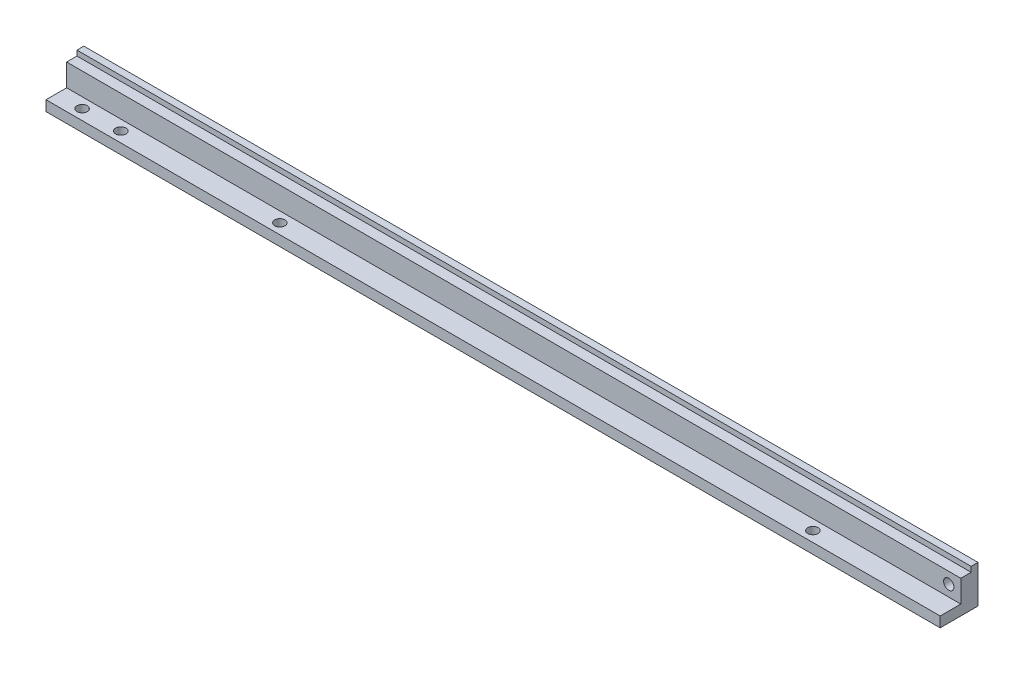
SolidWorks part; units mm, degrees
ref_plane "Спереди" through (0, 0, 0) normal (0, 0, 1) x (1, 0, 0)
ref_plane "Сверху" through (0, 0, 0) normal (0, 1, 0) x (1, 0, 0)
ref_plane "Справа" through (0, 0, 0) normal (1, 0, 0) x (0, 0, -1)
sketch "Эскиз1" plane through (0, 0, 0) normal (1, 0, 0) x (0, 0, -1)
  line L0 (0, 0) -> (-11, 0)
  line L1 (-11, 0) -> (-11, 3)
  line L2 (-11, 3) -> (-5, 3)
  line L3 (-5, 3) -> (-5, 9.5)
  line L4 (-5, 9.5) -> (-2, 9.5)
  line L5 (-2, 9.5) -> (-2, 11)
  line L6 (-2, 11) -> (0, 11)
  line L7 (0, 11) -> (0, 0)
  dimension "D1" = 5
  dimension "D2" = 11
  dimension "D3" = 3
  dimension "D4" = 6
  dimension "D5" = 6.5
  dimension "D6" = 11
  dimension "D7" = 1.5
  dimension "D8" = 2
extrude "Бобышка-Вытянуть1" add sketch "Эскиз1" along normal blind 260
sketch "Эскиз2" plane through (0, 0, 5) normal (0, 0, 1) x (1, 0, 0)
  line L1 (260, 9.5) -> (0, 9.5) construction
  line L2 (260, 9.5) -> (260, 3) construction
  circle A0 centre (256.5, 6.25) radius 1.5
  dimension "D1" = 3
  dimension "D2" = 3.5
  dimension "D3" = 3.25
extrude "Вырез-Вытянуть1" cut sketch "Эскиз2" against normal through all
sketch "Эскиз3" plane through (0, 3, 0) normal (0, 1, 0) x (1, 0, 0)
  line L1 (0, -5) -> (0, -11) construction
  line L2 (260, -11) -> (0, -11) construction
  circle A0 centre (7.5, -8) radius 1.5
  circle A1 centre (18.75, -8) radius 1.5
  dimension "D1" = 3
  dimension "D2" = 3
  dimension "D3" = 7.5
  dimension "D4" = 18.75
  dimension "D5" = 3
  dimension "D6" = 3
extrude "Вырез-Вытянуть2" cut sketch "Эскиз3" against normal through all
sketch "Эскиз5" plane through (0, 3, 0) normal (0, 1, 0) x (1, 0, 0)
  line L0 (0, -5) -> (0, -11) construction
  line L1 (260, -5) -> (260, -11) construction
  line L3 (260, -11) -> (0, -11) construction
  circle A0 centre (65, -8) radius 1.5
  circle A1 centre (220, -8) radius 1.5
  dimension "D1" = 3
  dimension "D4" = 3
  dimension "D2" = 65
  dimension "D3" = 3
  dimension "D5" = 3
  dimension "D6" = 40
extrude "Вырез-Вытянуть4" cut sketch "Эскиз5" against normal through all
